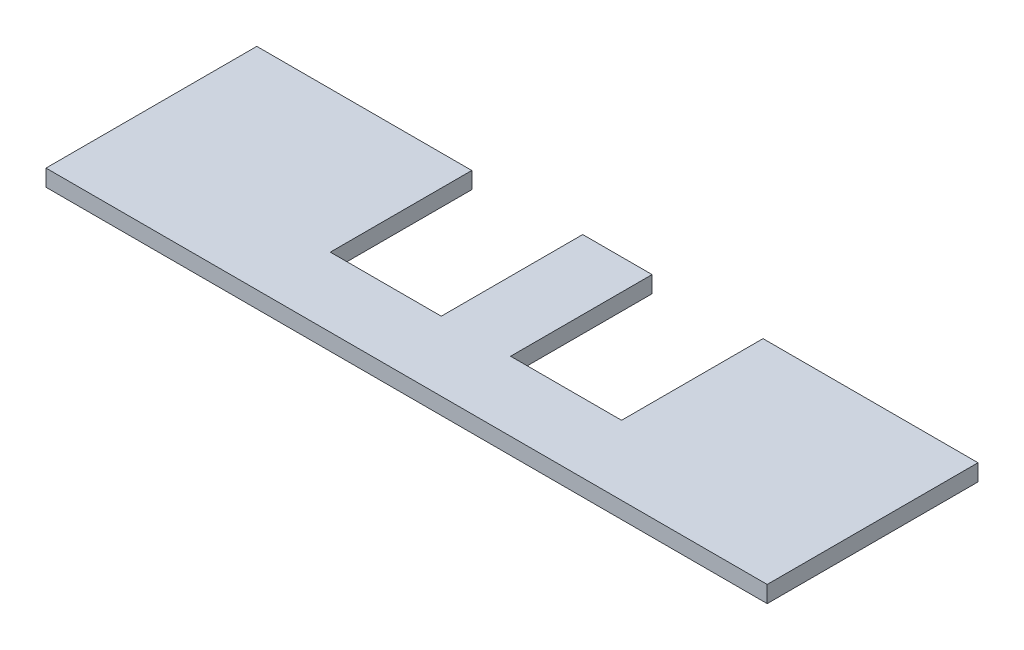
SolidWorks part; units mm, degrees
ref_plane "Front Plane" through (0, 0, 0) normal (0, 0, 1) x (1, 0, 0)
ref_plane "Top Plane" through (0, 0, 0) normal (0, 1, 0) x (1, 0, 0)
ref_plane "Right Plane" through (0, 0, 0) normal (1, 0, 0) x (0, 0, -1)
sketch "Sketch1" plane through (0, 0, 0) normal (0, 1, 0) x (1, 0, 0)
  line L1 (-65, -60) -> (65, -60)
  line L2 (-65, -60) -> (-65, 60)
  line L3 (-65, 60) -> (65, 60)
  line L4 (65, -60) -> (65, 60)
  line L5 (-65, -60) -> (65, 60) construction
  line L6 (-65, 60) -> (65, -60) construction
  point P0 (0, 0)
  dimension "D1" = 130
  dimension "D2" = 120
extrude "Boss-Extrude1" add sketch "Sketch1" along normal blind 3
sketch "Sketch2" plane through (0, 3, 0) normal (0, 1, 0) x (1, 0, 0)
  line L1 (-26.25, -47.5) -> (-6.25, -47.5)
  line L2 (-26.25, -47.5) -> (-26.25, 47.5)
  line L3 (-26.25, 47.5) -> (-6.25, 47.5)
  line L4 (-6.25, -47.5) -> (-6.25, 47.5)
  line L5 (-26.25, -47.5) -> (-6.25, 47.5) construction
  line L6 (-26.25, 47.5) -> (-6.25, -47.5) construction
  point P0 (-16.25, 0)
  dimension "D1" = 95
  dimension "D2" = 20
  dimension "D3" = 6.25
extrude "Cut-Extrude1" cut sketch "Sketch2" against normal through all both and the other way through all
mirror "Mirror1" about plane through (0, 0, 0) normal (1, 0, 0) of "Cut-Extrude1"
sketch "Sketch3" plane through (0, 3, 0) normal (0, 1, 0) x (1, 0, 0)
  circle A0 centre (44.5, 0) radius 1.6
  dimension "D1" = 3.2
  dimension "D2" = 44.5
extrude "Cut-Extrude2" cut sketch "Sketch3" against normal through all both and the other way through all
mirror "Mirror2" about plane through (0, 0, 0) normal (1, 0, 0) of "Cut-Extrude2"
sketch "Sketch4" plane through (0, 3, 0) normal (0, 1, 0) x (1, 0, 0)
  line L0 (-65, 60) -> (-65, -60) construction
  line L1 (-65, -22) -> (65, -22)
  line L2 (-65, -22) -> (-65, 60)
  line L3 (-65, 60) -> (65, 60)
  line L4 (65, -22) -> (65, 60)
  circle A0 centre (-44.5, 0) radius 1.6 construction
  dimension "D1" = 22
extrude "Cut-Extrude3" cut sketch "Sketch4" against normal through all both and the other way through all
